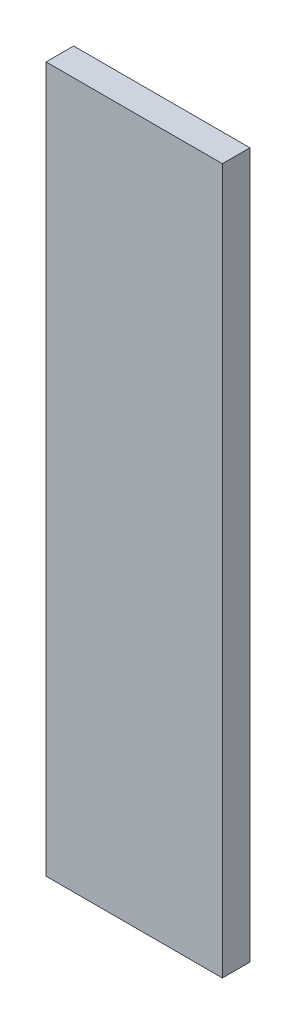
SolidWorks part; units mm, degrees
material "Pine"
ref_plane "Front Plane" through (0, 0, 0) normal (0, 0, 1) x (1, 0, 0)
ref_plane "Top Plane" through (0, 0, 0) normal (0, 1, 0) x (1, 0, 0)
ref_plane "Right Plane" through (0, 0, 0) normal (1, 0, 0) x (0, 0, -1)
sketch "Sketch1" plane through (0, 0, 0) normal (0, 0, 1) x (1, 0, 0)
  line L1 (-38.1, 409.5752) -> (38.1, 409.5752)
  line L2 (-38.1, 409.5752) -> (-38.1, 104.7752)
  line L3 (-38.1, 104.7752) -> (38.1, 104.7752)
  line L4 (38.1, 409.5752) -> (38.1, 104.7752)
extrude "Boss-Extrude1" add sketch "Sketch1" against normal up to surface (11.9062 mm away)
